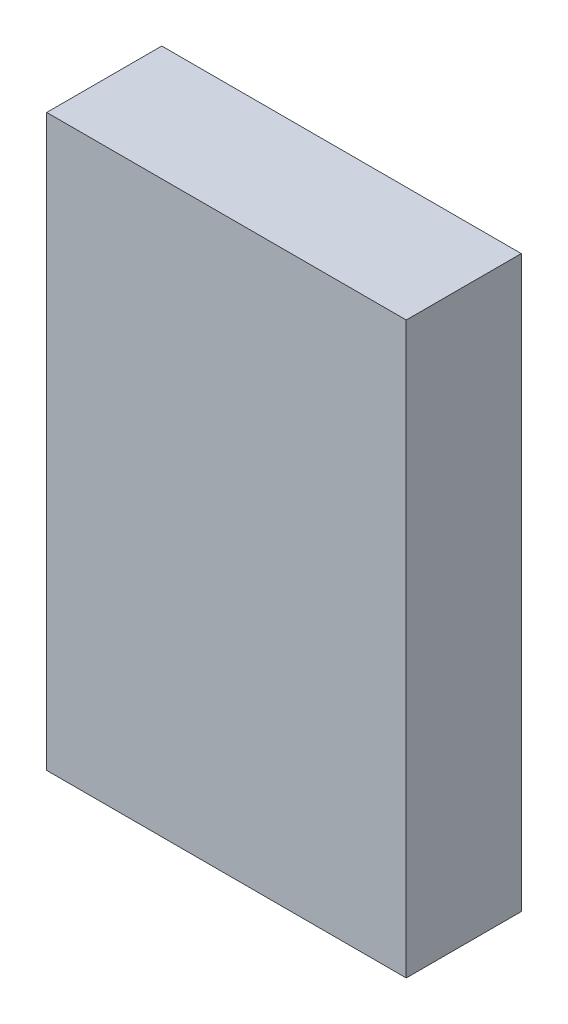
SolidWorks part; units mm, degrees
ref_plane "Front Plane" through (0, 0, 0) normal (0, 0, 1) x (1, 0, 0)
ref_plane "Top Plane" through (0, 0, 0) normal (0, 1, 0) x (1, 0, 0)
ref_plane "Right Plane" through (0, 0, 0) normal (1, 0, 0) x (0, 0, -1)
sketch "Sketch1" plane through (0, 0, 0) normal (0, 0, 1) x (1, 0, 0)
  line L0 (12.6482, 69.3506) -> (-2.2518, 69.3506) construction
  line L1 (0, 61.4256) -> (5, 61.4256)
  line L2 (0, 61.4256) -> (0, 69.3506)
  line L3 (0, 69.3506) -> (5, 69.3506)
  line L4 (5, 61.4256) -> (5, 69.3506)
  circle A0 centre (22.7232, 74.4256) radius 13 construction
  dimension "D1" = 5
extrude "Boss-Extrude1" add sketch "Sketch1" along normal blind 1.6
sketch "Sketch2" plane through (0, 69.3506, 0) normal (0, 1, 0) x (1, 0, 0)
  line L0 (0, -0.8) -> (5, -0.8) construction
  line L1 (0, -1.6) -> (0, 0) construction
  line L2 (5, -1.6) -> (5, 0) construction
